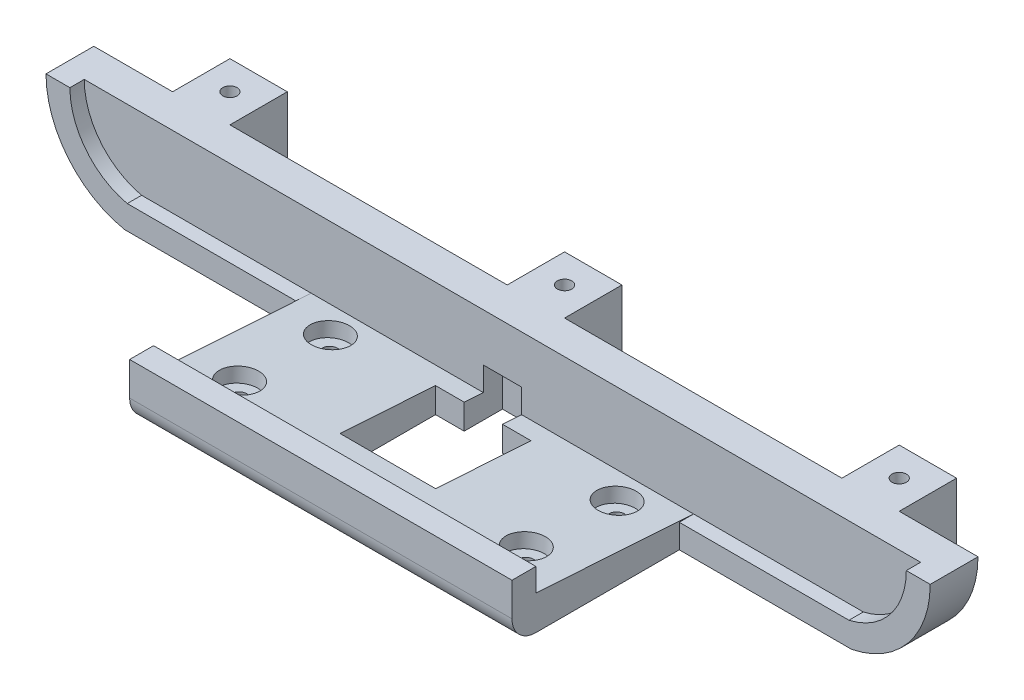
SolidWorks part; units mm, degrees
material "PMMA"
ref_plane "Front Plane" through (0, 0, 0) normal (0, 0, 1) x (1, 0, 0)
ref_plane "Top Plane" through (0, 0, 0) normal (0, 1, 0) x (1, 0, 0)
ref_plane "Right Plane" through (0, 0, 0) normal (1, 0, 0) x (0, 0, -1)
sketch "Schizzo1" plane through (0, 0, 0) normal (0, 0, 1) x (1, 0, 0)
  line L0 (-75.5, -15) -> (75.5, -15) construction
  line L1 (-75.5, 15) -> (75.5, 15) construction
  line L2 (-87.5, 15) -> (-87.5, -15) construction
  line L5 (87.5, 15) -> (87.5, -15) construction
  line L6 (-87.5, -15) -> (87.5, -15) construction
  line L7 (-75.5, 15) -> (-75.5, -15) construction
  line L8 (-87.5, 15) -> (87.5, 15) construction
  line L9 (-75.5, 15) -> (75.5, -15) construction
  line L10 (-76.0161, 20) -> (76.0161, 20)
  line L11 (-76.0161, -20) -> (76.0161, -20)
  arc A0 (-75.5, 15) -> (-75.5, -15) centre (-72.125, 0) ccw construction
  arc A1 (75.5, 15) -> (75.5, -15) centre (72.125, 0) cw construction
  arc A2 (76.0161, 20) -> (76.0161, -20) centre (72.125, 0) cw
  arc A3 (-76.0161, 20) -> (-76.0161, -20) centre (-72.125, 0) ccw
  point P12 (0, -15)
  point P13 (0, -15)
  point P14 (0, 0)
  dimension "D2" = 175
  dimension "D3" = 30
  dimension "D1" = 151
  dimension "D4" = 5
extrude "Estrusione-Estrusione1" add sketch "Schizzo1" along normal blind 10
sketch "Schizzo3" plane through (0, 0, 10) normal (0, 0, 1) x (1, 0, 0)
  line L0 (-75.5, -15) -> (75.5, -15)
  line L1 (-75.5, 15) -> (75.5, 15)
  line L2 (-87.5, 15) -> (-87.5, -15) construction
  line L3 (87.5, 15) -> (87.5, -15) construction
  line L4 (-87.5, -15) -> (87.5, -15) construction
  line L5 (-75.5, 15) -> (-75.5, -15) construction
  line L6 (-87.5, 15) -> (87.5, 15) construction
  line L7 (-75.5, 15) -> (75.5, -15) construction
  line L8 (-75.5, 15) -> (-75.5, -15) construction
  line L9 (-75.5, 15) -> (75.5, 15) construction
  arc A0 (-75.5, 15) -> (-75.5, -15) centre (-72.125, 0) ccw
  arc A1 (75.5, 15) -> (75.5, -15) centre (72.125, 0) cw
  point P12 (0, -15)
  point P13 (0, -15)
  dimension "D3" = 30
  dimension "D1" = 151
  dimension "D2" = 175
extrude "Taglio-Estrusione1" cut sketch "Schizzo3" against normal blind 3
sketch "Schizzo4" plane through (0, 0, 10) normal (0, 0, 1) x (1, 0, 0)
  line L1 (-40, -15) -> (40, -15)
  line L2 (-40, -15) -> (-40, -20)
  line L3 (-40, -20) -> (40, -20)
  line L4 (40, -15) -> (40, -20)
  line L7 (-75.5, -15) -> (75.5, -15) construction
  line L8 (-76.0161, -20) -> (76.0161, -20) construction
  point P8 (0, -20)
  dimension "D1" = 80
extrude "Estrusione-Estrusione2" add sketch "Schizzo4" along normal blind 35
sketch "Schizzo6" plane through (40, 0, 0) normal (1, 0, 0) x (0, 0, -1)
  line L0 (-40, -15) -> (-40, -12.81)
  line L1 (-45, -15) -> (-10, -15) construction
  line L2 (-40, -12.81) -> (-7, -15)
  line L3 (-7, -15) -> (-40, -15)
  line L4 (-45, -20) -> (-45, -15) construction
  dimension "D1" = 2.19
  dimension "D2" = 5
extrude "Estrusione-Estrusione4" add sketch "Schizzo6" against normal blind 80
sketch "Schizzo7" plane through (0, -15, 0) normal (0, 1, 0) x (1, 0, 0)
  line L1 (-40, -40) -> (40, -40)
  line L2 (-40, -40) -> (-40, -45)
  line L3 (-40, -45) -> (40, -45)
  line L4 (40, -40) -> (40, -45)
  dimension "D1" = 5
  dimension "D2" = 80
extrude "Estrusione-Estrusione5" add sketch "Schizzo7" along normal blind 7
sketch "Schizzo8" plane through (0, -20, 0) normal (0, -1, 0) x (1, 0, 0)
  line L0 (-40, 45) -> (-40, 10) construction
  line L2 (-76.0161, 0) -> (76.0161, 0) construction
  line L3 (-40, 45) -> (40, 45) construction
  line L4 (0, 45) -> (0, 0) construction
  circle A0 centre (-30, 13) radius 1.5
  circle A1 centre (-30, 32) radius 1.5
  circle A2 centre (30, 13) radius 1.5
  circle A3 centre (30, 32) radius 1.5
  dimension "D1" = 3
  dimension "D4" = 13
  dimension "D2" = 10
  dimension "D3" = 13
  dimension "D5" = 10
extrude "Taglio-Estrusione2" cut sketch "Schizzo8" against normal up to next
mirror "Specchia1" about plane through (0, 0, 0) normal (0, 1, 0) of "Estrusione-Estrusione2", "Estrusione-Estrusione4", "Estrusione-Estrusione5"
fillet "Raccordo1" radius 5 1 edges at (0, -20, 45)
fillet "Raccordo2" radius 5 1 edges at (0, 20, 45)
sketch "Schizzo9" plane through (0, -20, 0) normal (0, -1, 0) x (1, 0, 0)
  line L0 (-4, 11) -> (-4, 3)
  line L1 (-4, 3) -> (4, 3)
  line L2 (4, 3) -> (4, 11)
  line L3 (4, 11) -> (10, 11)
  line L4 (10, 11) -> (10, 31)
  line L5 (10, 31) -> (-10, 31)
  line L6 (-10, 31) -> (-10, 11)
  line L7 (-10, 11) -> (-4, 11)
  line L8 (0, 40) -> (0, 0) construction
  line L9 (40, 40) -> (-40, 40) construction
  line L10 (-76.0161, 0) -> (76.0161, 0) construction
  point P13 (0, 31)
  point P14 (0, 3)
  dimension "D1" = 8
  dimension "D2" = 3
  dimension "D3" = 20
  dimension "D4" = 20
  dimension "D5" = 8
extrude "Taglio-Estrusione3" cut sketch "Schizzo9" against normal blind 10 and the other way through all
sketch "Schizzo11" plane through (0, -15.3967, 1.0218) normal (0, 0.9978, -0.0662) x (1, 0, 0)
  circle A0 centre (-30, -12.0046) radius 4
  circle A1 centre (-30, -31.0464) radius 4
  circle A2 centre (30, -31.0464) radius 4
  circle A3 centre (30, -12.0046) radius 4
  ellipse E0 centre (-30, -12.0046) end of major axis (-30, -10.5013) minor radius 1.5 construction
  ellipse E1 centre (-30, -31.0464) end of major axis (-30, -32.5497) minor radius 1.5 construction
  ellipse E2 centre (30, -12.0046) end of major axis (30, -10.5013) minor radius 1.5 construction
  ellipse E3 centre (30, -31.0464) end of major axis (30, -29.5431) minor radius 1.5 construction
  dimension "D1" = 8
extrude "Taglio-Estrusione4" cut sketch "Schizzo11" against normal blind 3
sketch "Schizzo12" plane through (0, -20, 0) normal (0, -1, 0) x (1, 0, 0)
  line L0 (-76.0161, 10) -> (-76.0161, 0) construction
  line L1 (-76.0161, 0) -> (76.0161, 0) construction
  line L2 (76.0161, 0) -> (64.0161, 0)
  line L3 (76.0161, 0) -> (76.0161, -12)
  line L4 (76.0161, -12) -> (64.0161, -12)
  line L5 (64.0161, 0) -> (64.0161, -12)
  line L6 (76.0161, 10) -> (76.0161, 0) construction
  line L7 (-64.0161, 0) -> (-76.0161, 0)
  line L8 (-64.0161, 0) -> (-64.0161, -12)
  line L9 (-64.0161, -12) -> (-76.0161, -12)
  line L10 (-76.0161, 0) -> (-76.0161, -12)
  line L11 (6, 0) -> (-6, 0)
  line L12 (6, 0) -> (6, -12)
  line L13 (6, -12) -> (-6, -12)
  line L14 (-6, 0) -> (-6, -12)
  point P18 (0, 0)
  dimension "D1" = 12
  dimension "D2" = 12
  dimension "D3" = 12
  dimension "D4" = 12
  dimension "D5" = 12
  dimension "D6" = 12
extrude "Estrusione-Estrusione6" add sketch "Schizzo12" against normal up to surface (40 mm away) up to face at (0, 20, 15)
sketch "Schizzo13" plane through (0, -20, 0) normal (0, -1, 0) x (1, 0, 0)
  line L0 (-76.0161, -6) -> (76.0161, -6) construction
  line L1 (-76.0161, 0) -> (-76.0161, -12) construction
  line L2 (76.0161, -12) -> (76.0161, 0) construction
  line L3 (-70.0161, -12) -> (-70.0161, 10) construction
  line L4 (-76.0161, -12) -> (-64.0161, -12) construction
  line L5 (-76.0161, 10) -> (-40, 10) construction
  line L6 (0, -12) -> (0, 3) construction
  line L7 (-6, -12) -> (6, -12) construction
  line L8 (-4, 3) -> (4, 3) construction
  line L9 (70.0161, -12) -> (70.0161, 10) construction
  line L10 (64.0161, -12) -> (76.0161, -12) construction
  line L11 (40, 10) -> (76.0161, 10) construction
  circle A0 centre (-70.0161, -6) radius 1.5
  circle A1 centre (0, -6) radius 1.5
  circle A2 centre (70.0161, -6) radius 1.5
  dimension "D1" = 3
extrude "Taglio-Estrusione5" cut sketch "Schizzo13" against normal through all
sketch "Schizzo14" plane through (0, -20, 0) normal (0, -1, 0) x (1, 0, 0)
  circle A0 centre (-70.0161, -6) radius 4
  circle A1 centre (-70.0161, -6) radius 1.5 construction
  circle A2 centre (0, -6) radius 4
  circle A3 centre (70.0161, -6) radius 4
  circle A4 centre (70.0161, -6) radius 1.5 construction
  circle A5 centre (0, -6) radius 1.5 construction
  dimension "D1" = 8
extrude "Taglio-Estrusione6" cut sketch "Schizzo14" against normal blind 10
mirror "Specchia2" about plane through (0, 0, 0) normal (0, 1, 0) of "Taglio-Estrusione6"
other "TaglioSuperficie1"
